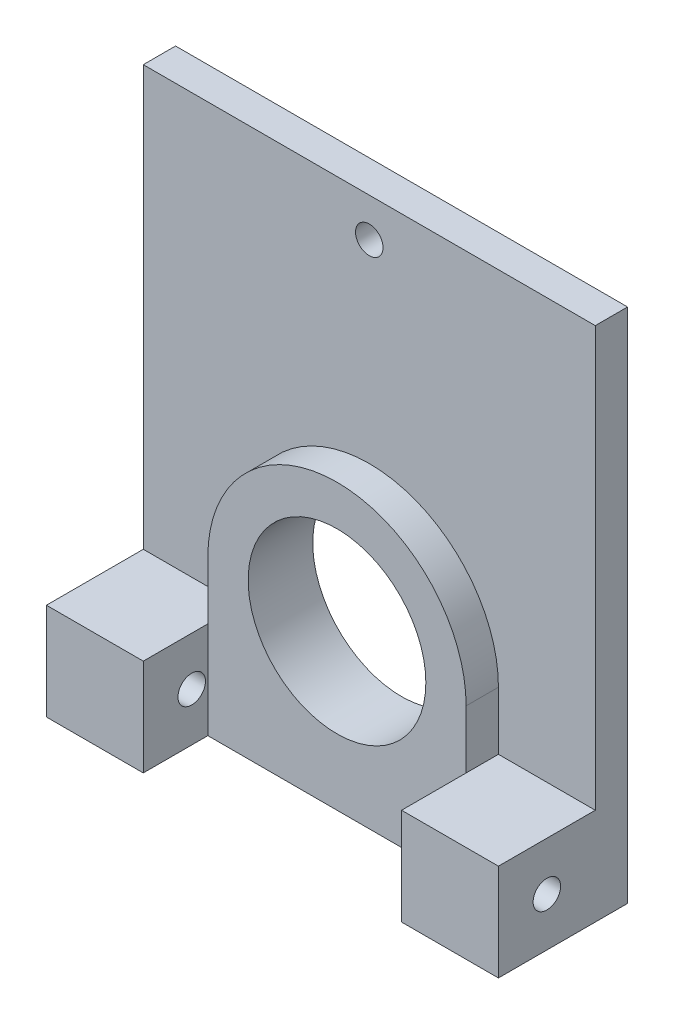
SolidWorks part; units mm, degrees
material "6061 Alloy"
ref_plane "Front Plane" through (0, 0, 0) normal (0, 0, 1) x (1, 0, 0)
ref_plane "Top Plane" through (0, 0, 0) normal (0, 1, 0) x (1, 0, 0)
ref_plane "Right Plane" through (0, 0, 0) normal (1, 0, 0) x (0, 0, -1)
sketch "Sketch1" plane through (0, 0, 0) normal (0, 0, 1) x (1, 0, 0)
  line L1 (-22.225, 25.4) -> (22.225, 25.4)
  line L2 (-22.225, 25.4) -> (-22.225, -25.4)
  line L3 (-22.225, -25.4) -> (22.225, -25.4)
  line L4 (22.225, 25.4) -> (22.225, -25.4)
  line L5 (-22.225, 25.4) -> (22.225, -25.4) construction
  line L6 (-22.225, -25.4) -> (22.225, 25.4) construction
  point P0 (0, 0)
  dimension "D1" = 44.45
  dimension "D2" = 50.8
extrude "Boss-Extrude1" add sketch "Sketch1" along normal blind 3.175
sketch "Sketch2" plane through (0, 0, 3.175) normal (0, 0, 1) x (1, 0, 0)
  line L0 (-12.7, -10.16) -> (-12.7, -25.4)
  line L1 (-22.225, -25.4) -> (22.225, -25.4) construction
  line L2 (12.7, -10.16) -> (12.7, -25.4)
  line L3 (-12.7, -25.4) -> (12.7, -25.4)
  arc A0 (12.7, -10.16) -> (-12.7, -10.16) centre (0, -10.16) ccw
  dimension "D1" = 25.4
  dimension "D2" = 15.24
extrude "Boss-Extrude2" add sketch "Sketch2" along normal blind 3.175
sketch "Sketch3" plane through (0, 0, 3.175) normal (0, 0, 1) x (1, 0, 0)
  line L0 (0, 0) -> (0, -25.4) construction
  line L1 (-22.225, -25.4) -> (-12.7, -25.4)
  line L2 (-22.225, -25.4) -> (-22.225, -15.875)
  line L3 (-22.225, -15.875) -> (-12.7, -15.875)
  line L4 (-12.7, -25.4) -> (-12.7, -15.875)
  line L5 (12.7, -25.4) -> (12.7, -15.875)
  line L6 (22.225, -15.875) -> (12.7, -15.875)
  line L7 (22.225, -25.4) -> (22.225, -15.875)
  line L8 (22.225, -25.4) -> (12.7, -25.4)
  line L9 (-12.7, -10.16) -> (-12.7, -25.4) construction
  dimension "D2" = 9.525
extrude "Boss-Extrude3" add sketch "Sketch3" along normal blind 9.525
sketch "Sketch4" plane through (0, 0, 6.35) normal (0, 0, 1) x (1, 0, 0)
  circle A0 centre (0, -10.16) radius 8.7376
  dimension "D1" = 17.4752
extrude "Cut-Extrude1" cut sketch "Sketch4" against normal through all
sketch "Sketch5" plane through (-22.225, 0, 0) normal (-1, 0, 0) x (0, 0, 1)
  line L0 (3.175, -15.875) -> (12.7, -25.4) construction
sketch "Sketch6" plane through (22.225, 0, 0) normal (1, 0, 0) x (0, 0, -1)
  line L0 (-3.175, -15.875) -> (-12.7, -25.4) construction
sketch "Sketch10" plane through (0, 0, 3.175) normal (0, 0, 1) x (1, 0, 0)
  line L0 (0, 2.54) -> (0, 25.4) construction
  line L1 (22.225, 25.4) -> (-22.225, 25.4) construction
  arc A0 (12.7, -10.16) -> (-12.7, -10.16) centre (0, -10.16) ccw construction
  circle A1 centre (0, -10.16) radius 8.7376 construction
  point P7 (0, 21.59)
  dimension "D1" = 31.75
hole_wizard "#6-32 Tapped Hole1" positions "3DSketch1" profile "Sketch8" tap size "#6-32" standard "ANSI Inch" end condition up to next
sketch3d "3DSketch1"
  line L0 (22.225, -15.875, 3.175) -> (22.225, -25.4, 12.7) construction
  line L1 (-22.225, -15.875, 3.175) -> (-22.225, -25.4, 12.7) construction
  point P0 (22.225, -20.6375, 7.9375)
  point P4 (-22.225, -20.6375, 7.9375)
  point P10 (0, 21.59, 3.175)
sketch "Sketch8" plane through (22.225, -20.6375, 7.9375) normal (0, 1, 0) x (0, 0, -1)
  line L0 (0, 0) -> (0, 9.525)
  line L1 (0, 9.525) -> (1.3525, 9.525)
  line L2 (1.3525, 9.525) -> (1.3525, 0)
  line L5 (1.3525, 0) -> (0, 0)
  line L11 (0, -6.35) -> (0, 107.95) construction
  dimension "Thru Tap Drill Dia." = 2.7051
  dimension "Thru Tap Drill Depth" = 9.525
cosmetic thread "Hole Thread4" parameters "D2"=3.5052
cosmetic thread "Hole Thread5" parameters "D2"=3.5052
cosmetic thread "Hole Thread6" parameters "D2"=3.5052
